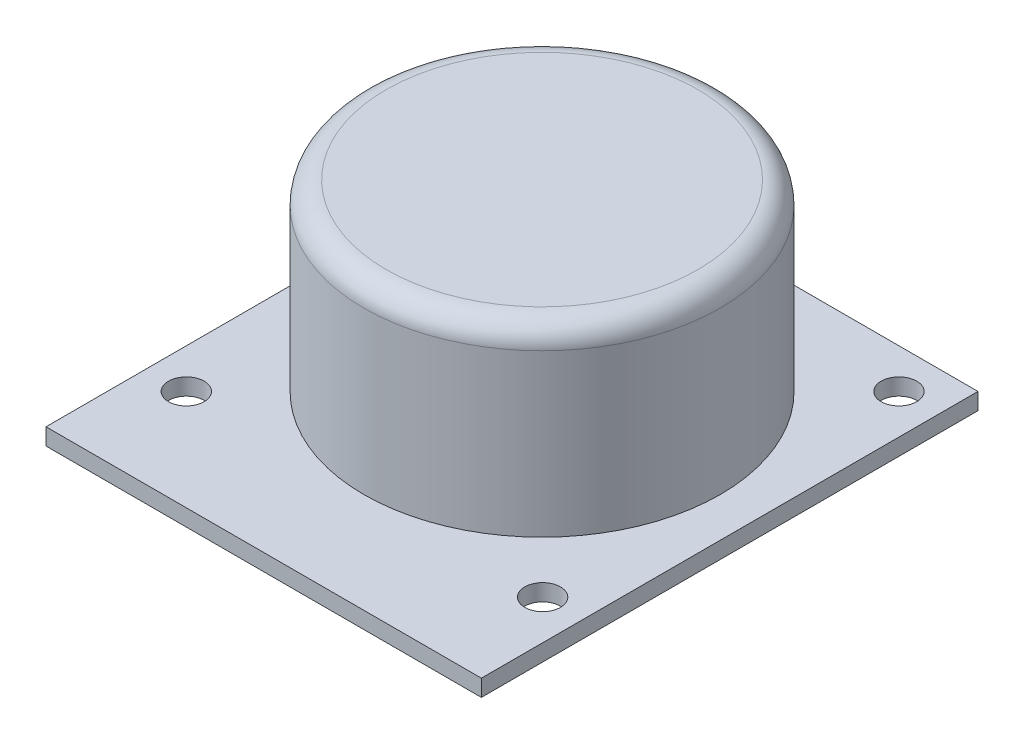
SolidWorks part; units mm, degrees
ref_plane "Front Plane" through (0, 0, 0) normal (0, 0, 1) x (1, 0, 0)
ref_plane "Top Plane" through (0, 0, 0) normal (0, 1, 0) x (1, 0, 0)
ref_plane "Right Plane" through (0, 0, 0) normal (1, 0, 0) x (0, 0, -1)
sketch "Sketch1" plane through (0, 0, 0) normal (0, 1, 0) x (1, 0, 0)
  line L0 (0, 0) -> (0, 44.6)
  line L1 (0, 44.6) -> (39.1, 44.6)
  line L2 (39.1, 44.6) -> (39.1, 0)
  line L3 (39.1, 0) -> (0, 0)
extrude "Boss-Extrude1" add sketch "Sketch1" along normal blind 1.5
sketch "Sketch2" plane through (0, 1.5, 0) normal (0, 1, 0) x (1, 0, 0)
  circle A4 centre (35.55, 9.05) radius 1.6
  circle A5 centre (35.55, 41.05) radius 1.6
  circle A6 centre (3.55, 41.05) radius 1.6
  circle A7 centre (3.55, 9.05) radius 1.6
extrude "Cut-Extrude1" cut sketch "Sketch2" against normal blind 1.5
sketch "Sketch3" plane through (0, 1.5, 0) normal (0, 1, 0) x (1, 0, 0)
  circle A0 centre (19.55, 25) radius 16
extrude "Boss-Extrude2" add sketch "Sketch3" along normal blind 16.5
fillet "Fillet1" radius 2 1 edges at (19.55, 18, -9)
